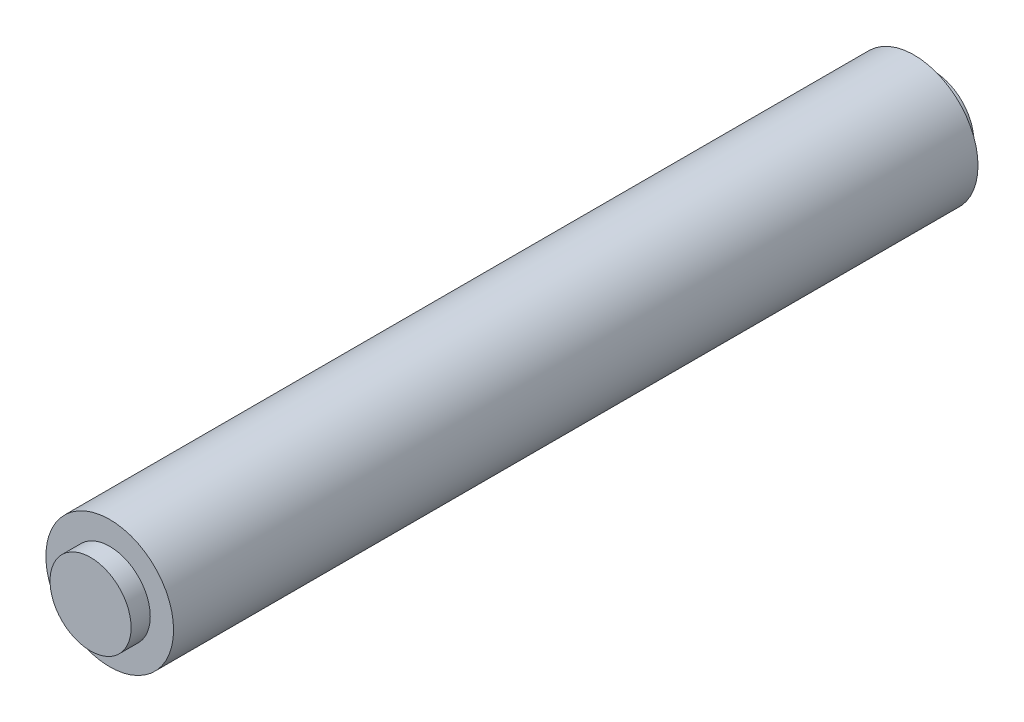
SolidWorks part; units mm, degrees
ref_plane "Front Plane" through (0, 0, 0) normal (0, 0, 1) x (1, 0, 0)
ref_plane "Top Plane" through (0, 0, 0) normal (0, 1, 0) x (1, 0, 0)
ref_plane "Right Plane" through (0, 0, 0) normal (1, 0, 0) x (0, 0, -1)
sketch "Sketch1" plane through (0, 0, 0) normal (0, 0, 1) x (1, 0, 0)
  circle A0 centre (0, 0) radius 3.175
  dimension "D1" = 6.35
extrude "Boss-Extrude1" add sketch "Sketch1" along normal mid plane 66
sketch "Sketch2" plane through (0, 0, 0) normal (0, 0, 1) x (1, 0, 0)
  circle A0 centre (0, 0) radius 5
  dimension "D1" = 10
extrude "Boss-Extrude2" add sketch "Sketch2" along normal mid plane 63 separate body
